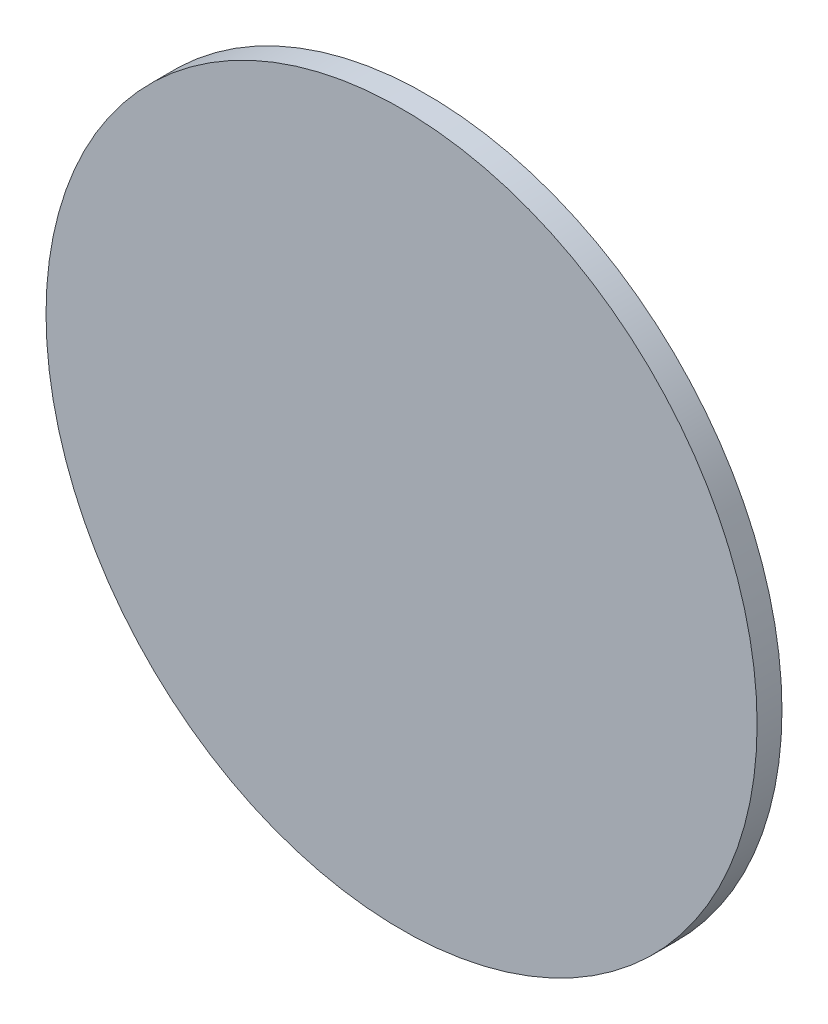
SolidWorks part; units mm, degrees
ref_plane "Plan de face" through (0, 0, 0) normal (0, 0, 1) x (1, 0, 0)
ref_plane "Plan de dessus" through (0, 0, 0) normal (0, 1, 0) x (1, 0, 0)
ref_plane "Plan de droite" through (0, 0, 0) normal (1, 0, 0) x (0, 0, -1)
sketch "Esquisse1" plane through (0, 0, 0) normal (0, 0, 1) x (1, 0, 0)
  circle A0 centre (0, 0) radius 143
  point P2 (0, 0)
  point P3 (0, 0)
  dimension "D1" = 286
extrude "Boss.-Extru.1" add sketch "Esquisse1" along normal blind 10
sketch "Esquisse2" plane through (0, 0, 0) normal (0, 0, -1) x (-1, 0, 0)
  line L1 (-143, 38.4735) -> (-128, 38.4735)
  line L2 (-143, 38.4735) -> (-143, -31.0265)
  line L3 (-143, -31.0265) -> (-128, -31.0265)
  line L4 (-128, 38.4735) -> (-128, -31.0265)
  line L5 (128, 34.7253) -> (143, 34.7253)
  line L6 (128, 34.7253) -> (128, -34.7747)
  line L7 (128, -34.7747) -> (143, -34.7747)
  line L8 (143, 34.7253) -> (143, -34.7747)
  line L9 (25, 25) -> (-25, 25)
  line L10 (25, 25) -> (25, -25)
  line L11 (25, -25) -> (-25, -25)
  line L12 (-25, 25) -> (-25, -25)
  circle A0 centre (38.0111, 57.9) radius 1.65
  circle A1 centre (0, -19.3) radius 1.65
  circle A2 centre (-73.8956, -38.6) radius 1.65
  circle A3 centre (0, -37.2521) radius 1.65
  circle A4 centre (-18.552, -37.2521) radius 1.65
  circle A5 centre (0, 38.6) radius 1.65
  circle A6 centre (0, 77.2) radius 1.65
  circle A7 centre (0, 57.9) radius 1.65
  circle A8 centre (0, -57.9) radius 1.65
  circle A10 centre (0, -77.2) radius 1.65
  circle A11 centre (-18.552, 38.6) radius 1.65
  circle A12 centre (-18.552, 77.2) radius 1.65
  circle A13 centre (-18.552, 57.9) radius 1.65
  circle A14 centre (-37.269, 77.2) radius 1.65
  circle A15 centre (19.6548, 77.2) radius 1.65
  circle A16 centre (19.6548, 57.9) radius 1.65
  circle A17 centre (-37.269, 57.9) radius 1.65
  circle A18 centre (19.6548, 38.6) radius 1.65
  circle A19 centre (-37.269, 38.6) radius 1.65
  circle A20 centre (-56.3928, 57.9) radius 1.65
  circle A21 centre (38.0111, 38.6) radius 1.65
  circle A22 centre (-73.8956, 38.6) radius 1.65
  circle A23 centre (-37.269, -38.6) radius 1.65
  circle A24 centre (-73.8956, 57.9) radius 1.65
  circle A25 centre (-56.3928, 38.6) radius 1.65
  circle A26 centre (-56.3928, 77.2) radius 1.65
  circle A27 centre (-73.8956, 77.2) radius 1.65
  circle A28 centre (38.0111, 77.2) radius 1.65
  circle A29 centre (-56.3928, -38.6) radius 1.65
  circle A30 centre (74.6314, -38.6) radius 1.65
  circle A31 centre (19.6548, -57.9) radius 1.65
  circle A32 centre (19.6548, -77.2) radius 1.65
  circle A33 centre (74.6314, -77.2) radius 1.65
  circle A34 centre (55.8996, -77.2) radius 1.65
  circle A35 centre (74.6314, -57.9) radius 1.65
  circle A36 centre (55.8996, -57.9) radius 1.65
  circle A37 centre (55.8996, -38.6) radius 1.65
  circle A38 centre (19.6548, -37.2521) radius 1.65
  circle A39 centre (38.0111, -77.2) radius 1.65
  circle A40 centre (38.0111, -38.6) radius 1.65
  circle A41 centre (38.0111, -57.9) radius 1.65
  circle A42 centre (-56.3928, -57.9) radius 1.65
  circle A43 centre (55.8996, 57.9) radius 1.65
  circle A44 centre (-37.269, -77.2) radius 1.65
  circle A45 centre (-56.3928, -77.2) radius 1.65
  circle A46 centre (74.6314, 77.2) radius 1.65
  circle A47 centre (74.6314, 38.6) radius 1.65
  circle A48 centre (55.8996, 77.2) radius 1.65
  circle A49 centre (-18.552, -77.2) radius 1.65
  circle A50 centre (-18.552, -57.9) radius 1.65
  circle A51 centre (55.8996, 38.6) radius 1.65
  circle A52 centre (-37.269, -57.9) radius 1.65
  circle A53 centre (74.6314, 57.9) radius 1.65
  circle A54 centre (-73.8956, 19.3) radius 1.65
  circle A55 centre (55.8996, 0) radius 1.65
  circle A56 centre (-56.3928, 0) radius 1.65
  circle A57 centre (-73.8956, -19.3) radius 1.65
  circle A58 centre (55.8996, -19.3) radius 1.65
  circle A59 centre (-56.3928, -19.3) radius 1.65
  circle A60 centre (74.6314, 19.5357) radius 1.65
  circle A61 centre (-56.3928, 19.3) radius 1.65
  circle A62 centre (-73.8956, -77.2) radius 1.65
  circle A63 centre (55.8996, 19.3) radius 1.65
  circle A64 centre (-73.8956, -57.9) radius 1.65
  circle A65 centre (-73.8956, 0) radius 1.65
  circle A67 centre (38.0111, 0) radius 1.65
  circle A68 centre (38.0111, -19.3) radius 1.65
  circle A73 centre (38.0111, 19.3) radius 1.65
  circle A74 centre (74.6314, -19.3) radius 1.65
  circle A76 centre (74.6314, 0) radius 1.65
  circle A85 centre (-37.269, -19.3) radius 1.65
  circle A87 centre (-37.269, 0) radius 1.65
  circle A89 centre (-37.269, 19.3) radius 1.65
  circle A90 centre (-18.552, -19.3) radius 1.65
  circle A91 centre (19.6548, -19.3) radius 1.65
  circle A92 centre (-18.552, 0) radius 1.65
  circle A93 centre (0, 0) radius 1.65
  circle A94 centre (19.6548, 0) radius 1.65
  circle A95 centre (0, 19.3) radius 1.65
  circle A96 centre (19.6548, 19.3) radius 1.65
  circle A97 centre (-18.552, 19.3) radius 1.65
  point P14 (0, 0)
  point P15 (0, 0)
  point P18 (0, 0)
  point P19 (0, 0)
  point P20 (0, 0)
  point P23 (-25, 45)
  point P28 (-8.4559, 51.9119)
  point P29 (-25, 59.7788)
  point P30 (0, 34.7253)
  point P31 (0, -37.2521)
  point P32 (0, 50.7112)
  point P33 (0, 65.2044)
  point P36 (0, -63.1908)
  point P37 (0, -50.1431)
  point P38 (0, 79.9578)
  point P39 (0, 0)
  point P40 (0, 0)
  point P41 (0, 0)
  point P44 (0, -61.6913)
  point P45 (-18.552, -37.2521)
  point P52 (-18.552, 65.2044)
  point P53 (-18.552, 50.7112)
  point P54 (-18.552, 34.7253)
  point P67 (-37.269, 65.2044)
  point P68 (-37.269, 50.7112)
  point P69 (-37.269, 34.7253)
  point P70 (19.6548, 65.2044)
  point P71 (19.6548, 50.7112)
  point P72 (19.6548, 34.7253)
  point P97 (38.0111, 65.2044)
  point P98 (38.0111, 50.7112)
  point P99 (38.0111, 34.7253)
  point P100 (-56.3928, 65.2044)
  point P101 (-56.3928, 50.7112)
  point P102 (-60.9979, 34.7253)
  point P103 (0, 0)
  point P104 (0, 0)
  point P105 (-56.3928, 34.7253)
  point P106 (-56.3928, -37.2521)
  point P107 (-37.269, -37.2521)
  point P108 (-73.8956, -37.2521)
  point P109 (-73.8956, 65.2044)
  point P110 (-73.8956, 50.7112)
  point P111 (-73.8956, 34.7253)
  point P136 (19.6548, -37.2521)
  point P137 (38.0111, -37.2521)
  point P138 (55.8996, -37.2521)
  point P139 (74.6314, -37.2521)
  point P140 (19.6548, -50.1431)
  point P141 (19.6548, -61.6913)
  point P142 (38.0111, -50.1431)
  point P143 (38.0111, -61.6913)
  point P144 (55.8996, -50.1431)
  point P145 (55.8996, -61.6913)
  point P146 (74.6314, -50.1431)
  point P147 (74.6314, -61.6913)
  point P172 (55.8996, 65.2044)
  point P173 (74.6314, 65.2044)
  point P174 (0, 0)
  point P175 (55.8996, 50.7112)
  point P176 (55.8996, 34.7253)
  point P177 (74.6314, 50.7112)
  point P178 (74.6314, 34.7253)
  point P179 (-18.552, -61.6913)
  point P180 (-18.552, -50.1431)
  point P181 (-37.269, -61.6913)
  point P182 (-37.269, -50.1431)
  point P183 (-56.3928, -50.1431)
  point P184 (-56.3928, -61.6913)
  point P209 (-73.8956, -50.1431)
  point P210 (-73.8956, -61.6913)
  point P211 (-73.8956, 19.5357)
  point P212 (-73.8956, -19.4444)
  point P213 (-73.8956, 3.7235)
  point P214 (-56.3928, 19.5357)
  point P215 (-56.3928, 0)
  point P216 (-56.3928, -19.4444)
  point P217 (55.8996, 19.5357)
  point P218 (55.8996, 0)
  point P219 (55.8996, -19.4444)
  point P220 (74.6314, 19.5357)
  point P221 (0, 0)
  point P222 (-56.3928, 0)
  point P227 (0, 0)
  point P228 (0, 0)
  point P229 (0, 0)
  point P230 (0, 0)
  point P231 (0, 0)
  point P232 (0, 0)
  point P233 (0, 0)
  point P234 (-264.6467, -153.2155)
  point P239 (0, 0)
  point P240 (0, 0)
  point P243 (-88.4277, -54.2283)
  point P244 (0, 0)
  point P245 (74.6314, 0)
  point P246 (74.6314, -19.4444)
  point P247 (38.0111, 19.5357)
  point P248 (38.0111, 0)
  point P249 (38.0111, -19.4444)
  point P250 (0, 0)
  point P251 (0, 0)
  point P252 (0, 0)
  point P253 (-66.538, 59.3144)
  point P254 (0, 0)
  point P255 (0, 0)
  point P256 (0, 0)
  point P257 (0, 0)
  point P258 (0, 0)
  point P259 (-38.8065, 19.8989)
  point P262 (-33.4824, 19.3)
  point P263 (0, 0)
  point P264 (0, 0)
  point P265 (0, 0)
  point P266 (0, 0)
  point P267 (0, 0)
  point P268 (0, 0)
  point P269 (0, 0)
  point P270 (0, 0)
  point P271 (0, 0)
  point P274 (0, 0)
  point P275 (-128, 73.7401)
  point P278 (-202.8001, -66.3761)
  point P279 (-37.269, 19.3)
  point P280 (-37.269, 0)
  point P281 (-37.269, -19.3)
  point P282 (-37.269, 19.3)
  point P283 (-86.118, 62.3542)
  point P284 (-18.552, 77.2)
  point P285 (0, 77.2)
  point P286 (19.6548, 77.2)
  point P287 (19.6548, 57.9)
  point P288 (19.6548, 38.6)
  point P289 (0, 57.9)
  point P290 (-18.552, 57.9)
  point P291 (-18.552, 38.6)
  point P292 (0, 38.6)
  point P293 (74.6314, 77.2)
  point P294 (74.6314, 57.9)
  point P295 (74.6314, 38.6)
  point P296 (0, 0)
  point P297 (19.6548, -77.2)
  point P298 (19.6548, -57.9)
  point P299 (0, -77.2)
  point P300 (-18.552, -77.2)
  point P301 (-18.552, -57.9)
  point P302 (0, -57.9)
  point P305 (0, -19.3)
  point P308 (-18.552, -19.3)
  point P311 (19.6548, -19.3)
  point P314 (-18.552, 0)
  point P317 (0, 0)
  point P321 (19.6548, 0)
  point P324 (0, 19.3)
  point P327 (19.6548, 19.3)
  point P330 (-18.552, 19.3)
  dimension "D1" = 69.5
  dimension "D2" = 15
  dimension "D3" = 103
  dimension "D4" = 15
  dimension "D5" = 69.5
  dimension "D6" = 103
  dimension "D10" = 25
